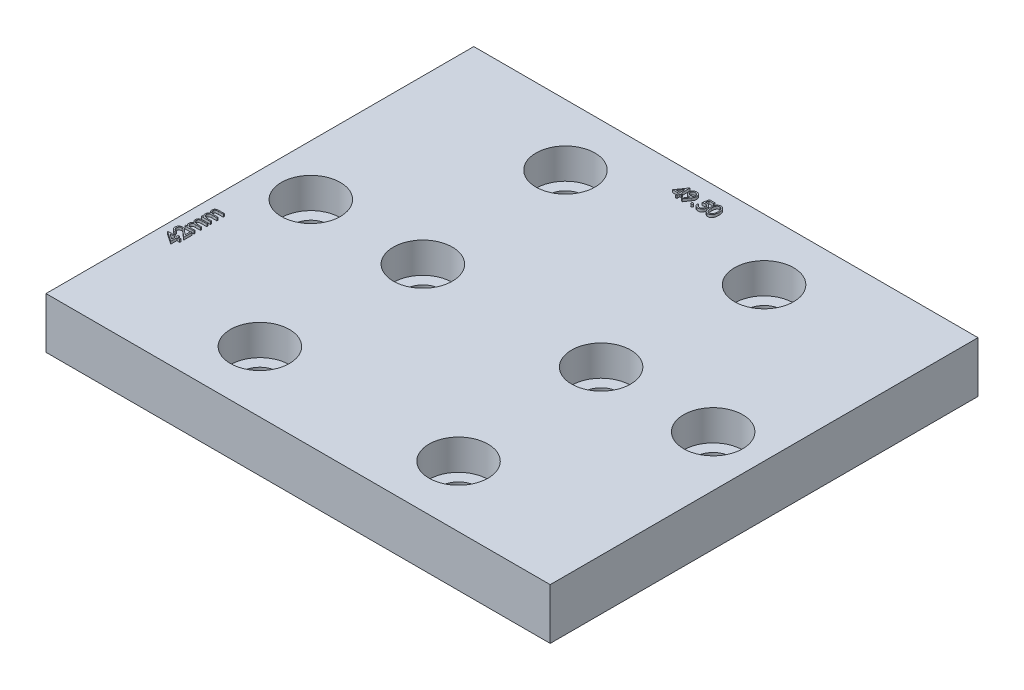
SolidWorks part; units mm, degrees
ref_plane "Front Plane" through (0, 0, 0) normal (0, 0, 1) x (1, 0, 0)
ref_plane "Top Plane" through (0, 0, 0) normal (0, 1, 0) x (1, 0, 0)
ref_plane "Right Plane" through (0, 0, 0) normal (1, 0, 0) x (0, 0, -1)
sketch "Sketch1" plane through (0, 0, 0) normal (0, 1, 0) x (1, 0, 0)
  line L1 (24.75, -21) -> (-24.75, -21)
  line L2 (24.75, -21) -> (24.75, 21)
  line L3 (24.75, 21) -> (-24.75, 21)
  line L4 (-24.75, -21) -> (-24.75, 21)
  line L5 (24.75, -21) -> (-24.75, 21) construction
  line L6 (24.75, 21) -> (-24.75, -21) construction
  point P0 (0, 0)
  dimension "D1" = 42
  dimension "D2" = 49.5
extrude "Boss-Extrude1" add sketch "Sketch1" along normal blind 5
sketch "Sketch2" plane through (0, 5, 0) normal (0, 1, 0) x (1, 0, 0)
  line L0 (-24.75, 21) -> (-24.75, -21) construction
  line L1 (24.75, 21) -> (-24.75, 21) construction
  line L2 (24.75, -21) -> (24.75, 21) construction
  line L3 (-24.75, -21) -> (24.75, -21) construction
  circle A0 centre (-9.75, 15) radius 1.75
  circle A1 centre (9.75, 15) radius 1.75
  circle A2 centre (19.75, 0) radius 1.75
  circle A3 centre (-19.75, 0) radius 1.75
  circle A4 centre (-9.75, -15) radius 1.75
  circle A5 centre (9.75, -15) radius 1.75
  circle A6 centre (-8.75, 0) radius 1.75
  circle A7 centre (8.75, 0) radius 1.75
  dimension "D1" = 3.5
  dimension "D2" = 15
  dimension "D3" = 6
  dimension "D4" = 15
  dimension "D5" = 6
  dimension "D6" = 15
  dimension "D7" = 6
  dimension "D8" = 6
  dimension "D9" = 15
  dimension "D10" = 5
  dimension "D11" = 5
  dimension "D12" = 3.5
  dimension "D13" = 21
  dimension "D14" = 21
  dimension "D15" = 3.5
  dimension "D16" = 21
  dimension "D17" = 21
  dimension "D18" = 11
  dimension "D19" = 11
extrude "Cut-Extrude1" cut sketch "Sketch2" against normal through all
sketch "Sketch3" plane through (-31.5902, 5, -10.7231) normal (0, 1, 0) x (0, 0, -1)
  text T0 "42mm" font "Century Gothic" height 1.25
extrude "Boss-Extrude2" add sketch "Sketch3" along normal blind 0.25
sketch "Sketch5" plane through (-2.6129, 5, -18.0475) normal (0, 1, 0) x (1, 0, 0)
  text T0 "49.50" font "Century Gothic" height 1.25
extrude "Boss-Extrude3" add sketch "Sketch5" along normal blind 0.25
sketch "Sketch6" plane through (0, 5, 0) normal (0, 1, 0) x (1, 0, 0)
  circle A0 centre (-9.75, 15) radius 2.9
  circle A1 centre (9.75, 15) radius 2.9
  circle A2 centre (-8.75, 0) radius 2.9
  circle A3 centre (-19.75, 0) radius 2.9
  circle A4 centre (-9.75, -15) radius 2.9
  circle A5 centre (9.75, -15) radius 2.9
  circle A6 centre (8.75, 0) radius 2.9
  circle A7 centre (19.75, 0) radius 2.9
  dimension "D1" = 5.8
extrude "Cut-Extrude2" cut sketch "Sketch6" against normal blind 3 and the other way through all
